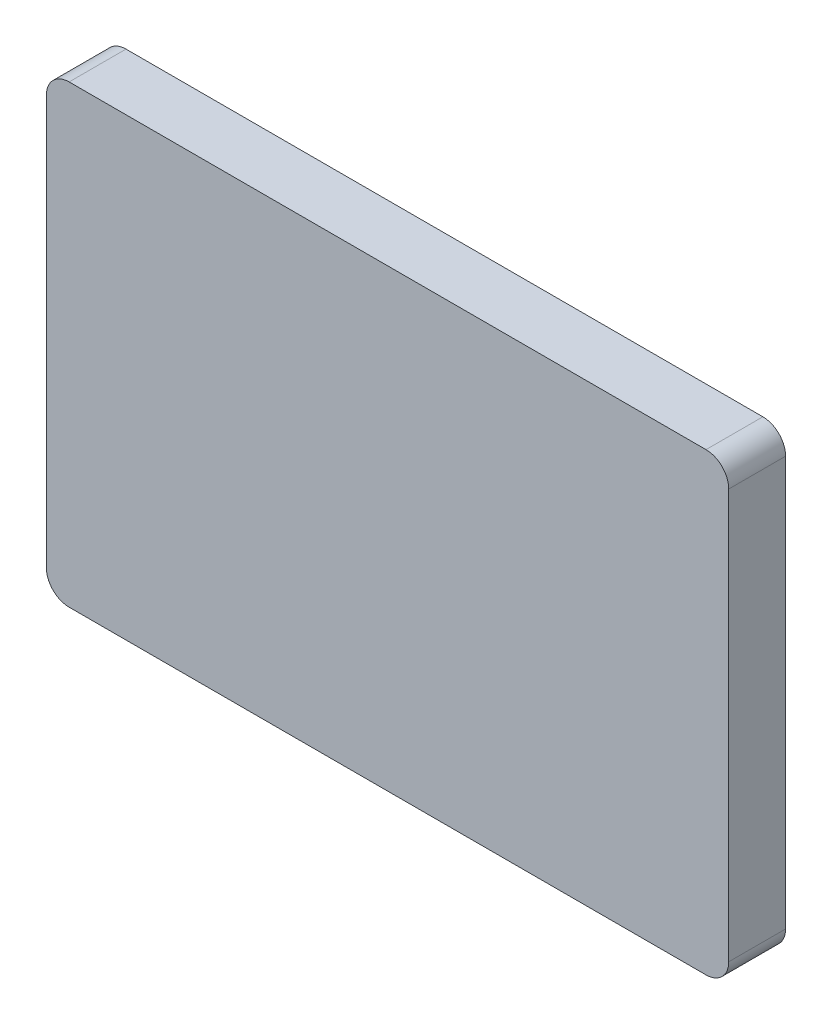
SolidWorks part; units mm, degrees
material "Polyurethane Foam Flexible"
ref_plane "Front Plane" through (0, 0, 0) normal (0, 0, 1) x (1, 0, 0)
ref_plane "Top Plane" through (0, 0, 0) normal (0, 1, 0) x (1, 0, 0)
ref_plane "Right Plane" through (0, 0, 0) normal (1, 0, 0) x (0, 0, -1)
sketch "Sketch1" plane through (0, 0, 0) normal (0, 0, 1) x (1, 0, 0)
  line L1 (-38.1, -25.4) -> (38.1, -25.4)
  line L2 (-38.1, -25.4) -> (-38.1, 25.4)
  line L3 (-38.1, 25.4) -> (38.1, 25.4)
  line L4 (38.1, -25.4) -> (38.1, 25.4)
  line L5 (-38.1, -25.4) -> (38.1, 25.4) construction
  line L6 (-38.1, 25.4) -> (38.1, -25.4) construction
  point P0 (0, 0)
  dimension "D1" = 50.8
  dimension "D2" = 76.2
extrude "Boss-Extrude1" add sketch "Sketch1" along normal blind 6.35
fillet "Fillet1" radius 2.54 4 edges at (38.1, 25.4, 3.175) (38.1, -25.4, 3.175) (-38.1, -25.4, 3.175) (-38.1, 25.4, 3.175)
